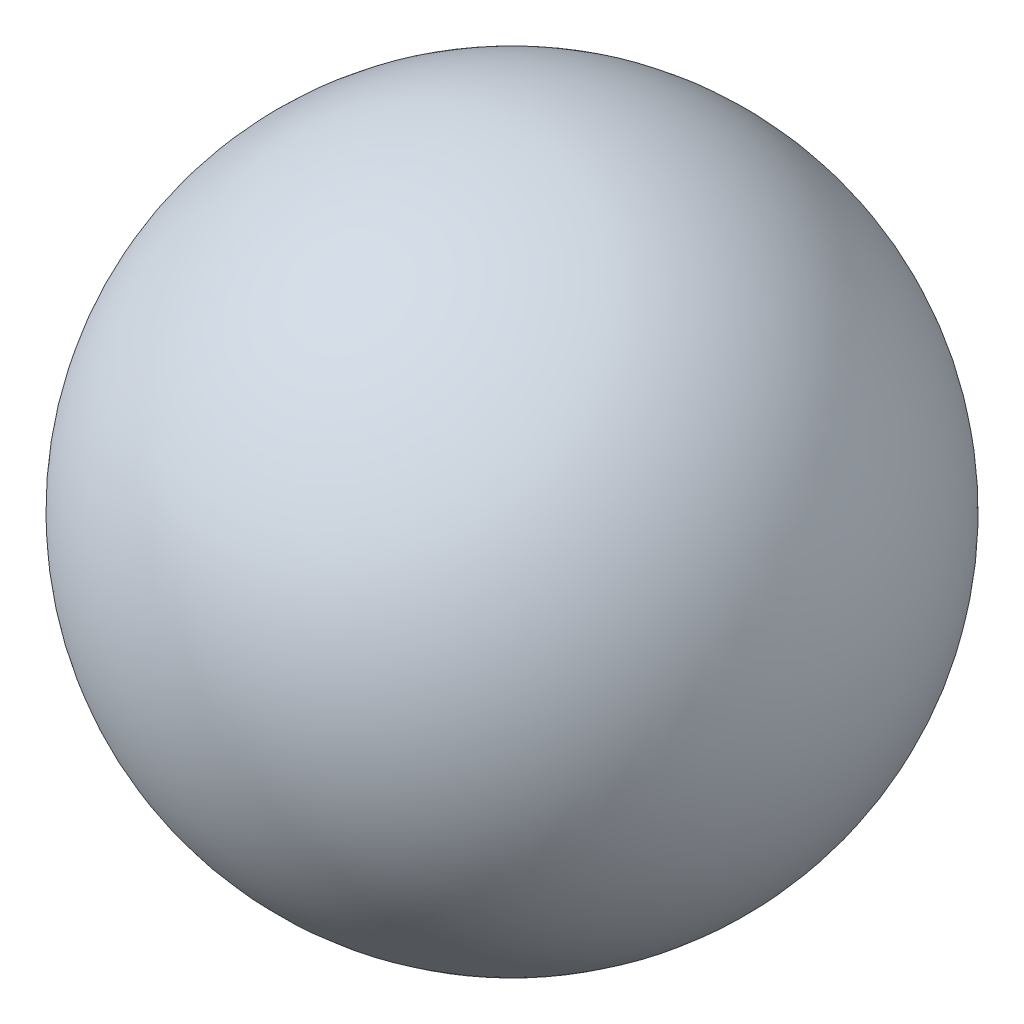
SolidWorks part; units mm, degrees
ref_plane "Ebene vorne" through (0, 0, 0) normal (0, 0, 1) x (1, 0, 0)
ref_plane "Ebene oben" through (0, 0, 0) normal (0, 1, 0) x (1, 0, 0)
ref_plane "Ebene rechts" through (0, 0, 0) normal (1, 0, 0) x (0, 0, -1)
sketch "Sketch2" plane through (0, 0, 0) normal (0, 0, 1) x (1, 0, 0)
  line L0 (0, 40) -> (0, -37.9967)
  line L1 (0, -37.9967) -> (12.5, -37.9967)
  arc A0 (0, 40) -> (12.5, -37.9967) centre (0, 0) cw
  dimension "D1" = 40
  dimension "D3" = 12.5
revolve "Revolve1" add sketch "Sketch2" angle 360 about L0
shell "Shell5" thickness 1.25
